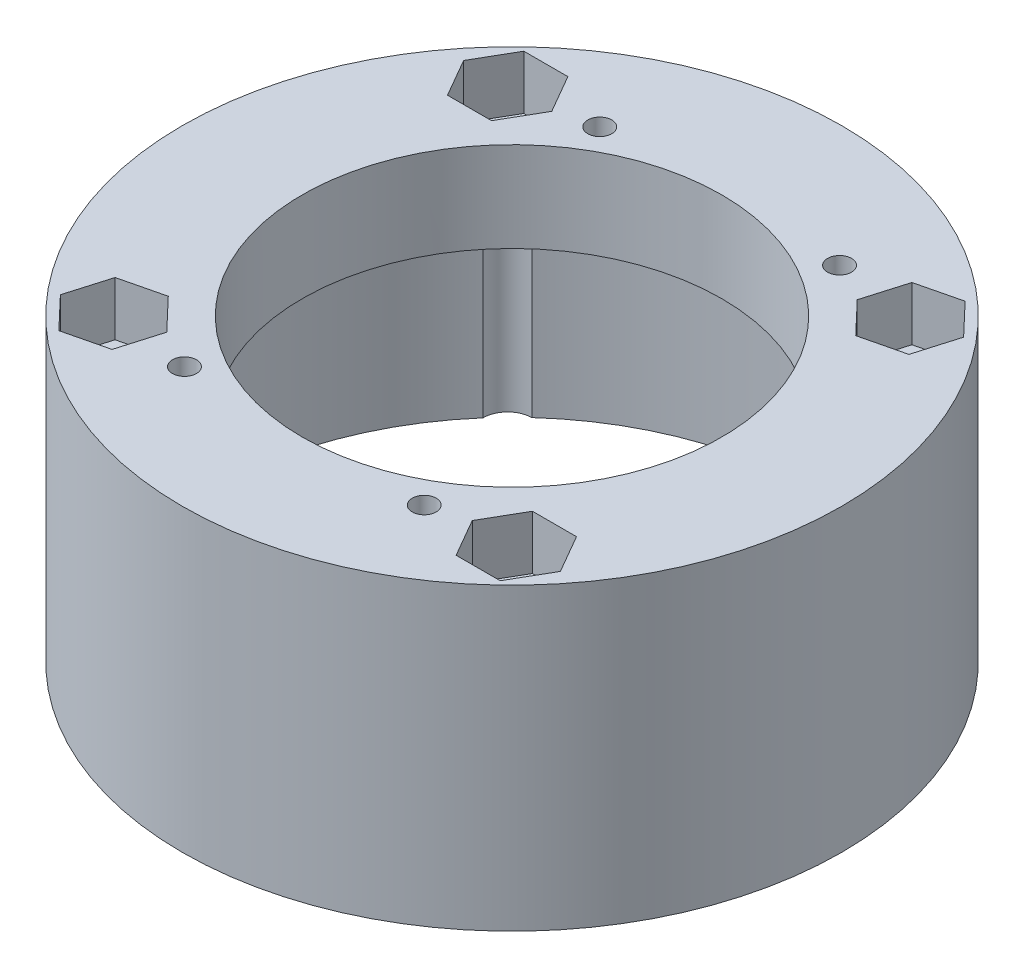
SolidWorks part; units mm, degrees
ref_plane "Спереди" through (0, 0, 0) normal (0, 0, 1) x (1, 0, 0)
ref_plane "Сверху" through (0, 0, 0) normal (0, 1, 0) x (1, 0, 0)
ref_plane "Справа" through (0, 0, 0) normal (1, 0, 0) x (0, 0, -1)
sketch "Sketch1" plane through (0, 0, 0) normal (0, 1, 0) x (1, 0, 0)
  circle A0 centre (0, 0) radius 55
  dimension "D1" = 110
extrude "Boss-Extrude1" add sketch "Sketch1" along normal blind 40
shell "Shell1" thickness 5
sketch "Sketch2" plane through (0, 35, 0) normal (0, -1, 0) x (1, 0, 0)
  circle A0 centre (0, 0) radius 35
  dimension "D1" = 70
extrude "Cut-Extrude1" cut sketch "Sketch2" against normal through all
sketch "Sketch3" plane through (0, 40, 0) normal (0, 1, 0) x (1, 0, 0)
  line L1 (20, 34.641) -> (-20, 34.641) construction
  line L2 (20, 34.641) -> (20, -34.641) construction
  line L3 (20, -34.641) -> (-20, -34.641) construction
  line L4 (-20, 34.641) -> (-20, -34.641) construction
  line L5 (20, 34.641) -> (-20, -34.641) construction
  line L6 (20, -34.641) -> (-20, 34.641) construction
  circle A0 centre (0, 0) radius 40 construction
  circle A1 centre (-20, -34.641) radius 2
  circle A2 centre (-20, 34.641) radius 2
  circle A3 centre (20, 34.641) radius 2
  circle A4 centre (20, -34.641) radius 2
  dimension "D1" = 80
  dimension "D3" = 4
  dimension "D2" = 40
extrude "Cut-Extrude2" cut sketch "Sketch3" against normal through all
sketch "Sketch4" plane through (0, 40, 0) normal (0, 1, 0) x (1, 0, 0)
  line L0 (-39.3095, -38.4677) -> (39.3095, 38.4677) construction
  line L1 (-39.3095, 38.4677) -> (39.3095, -38.4677) construction
  line L2 (33.5917, -32.8724) -> (-33.5917, -32.8724) construction
  circle A0 centre (0, 0) radius 55
  circle A1 centre (0, 0) radius 35
  circle A2 centre (-33.5917, -32.8724) radius 4.1
  circle A3 centre (-33.5917, 32.8724) radius 4.1
  circle A4 centre (33.5917, 32.8724) radius 4.1
  circle A5 centre (33.5917, -32.8724) radius 4.1
  circle A6 centre (0, 0) radius 47 construction
  circle A7 centre (0, 0) radius 55 construction
  circle A8 centre (20, 34.641) radius 2
  circle A9 centre (20, -34.641) radius 2
  circle A10 centre (-20, -34.641) radius 2
  circle A11 centre (-20, 34.641) radius 2
  point P31 (0, -47)
  point P32 (-46.989, 1.1903)
  point P33 (34.5449, 31.8693)
  dimension "D2" = 8.2
  dimension "D3" = 8
  dimension "D1" = 91.24
extrude "Boss-Extrude2" add sketch "Sketch4" along normal blind 10
sketch "Sketch5" plane through (0, 50, 0) normal (0, 1, 0) x (1, 0, 0)
  circle A0 centre (-33.5917, -32.8724) radius 4.1
  circle A1 centre (-33.5917, 32.8724) radius 4.1
  circle A2 centre (33.5917, 32.8724) radius 4.1
  circle A3 centre (33.5917, -32.8724) radius 4.1
extrude "Cut-Extrude3" cut sketch "Sketch5" against normal through all
sketch "Sketch6" plane through (0, 50, 0) normal (0, 1, 0) x (1, 0, 0)
  line L1 (37.2667, -26.5071) -> (29.9167, -26.5071)
  line L2 (29.9167, -26.5071) -> (26.2417, -32.8724)
  line L3 (26.2417, -32.8724) -> (29.9167, -39.2377)
  line L4 (29.9167, -39.2377) -> (37.2667, -39.2377)
  line L5 (37.2667, -39.2377) -> (40.9417, -32.8724)
  line L6 (40.9417, -32.8724) -> (37.2667, -26.5071)
  line L7 (-28.5219, -38.194) -> (-26.4482, -31.1426)
  line L8 (-26.4482, -31.1426) -> (-31.5181, -25.821)
  line L9 (-31.5181, -25.821) -> (-38.6616, -27.5509)
  line L10 (-38.6616, -27.5509) -> (-40.7353, -34.6023)
  line L11 (-40.7353, -34.6023) -> (-35.6654, -39.9238)
  line L12 (-35.6654, -39.9238) -> (-28.5219, -38.194)
  line L13 (-26.2417, 32.8724) -> (-29.9167, 39.2377)
  line L14 (-29.9167, 39.2377) -> (-37.2667, 39.2377)
  line L15 (-37.2667, 39.2377) -> (-40.9417, 32.8724)
  line L16 (-40.9417, 32.8724) -> (-37.2667, 26.5071)
  line L17 (-37.2667, 26.5071) -> (-29.9167, 26.5071)
  line L18 (-29.9167, 26.5071) -> (-26.2417, 32.8724)
  line L19 (31.5181, 25.821) -> (38.6616, 27.5509)
  line L20 (38.6616, 27.5509) -> (40.7353, 34.6023)
  line L21 (40.7353, 34.6023) -> (35.6654, 39.9238)
  line L22 (35.6654, 39.9238) -> (28.5219, 38.194)
  line L23 (28.5219, 38.194) -> (26.4482, 31.1426)
  line L24 (26.4482, 31.1426) -> (31.5181, 25.821)
  circle A0 centre (33.5917, -32.8724) radius 7.35 construction
  circle A1 centre (-33.5917, -32.8724) radius 7.35 construction
  circle A2 centre (-33.5917, 32.8724) radius 7.35 construction
  circle A3 centre (33.5917, 32.8724) radius 7.35 construction
  point P28 (35.8663, 3.1556)
  point P37 (-35, 4.8047)
  dimension "D1" = 14.7
extrude "Cut-Extrude4" cut sketch "Sketch6" against normal blind 9
